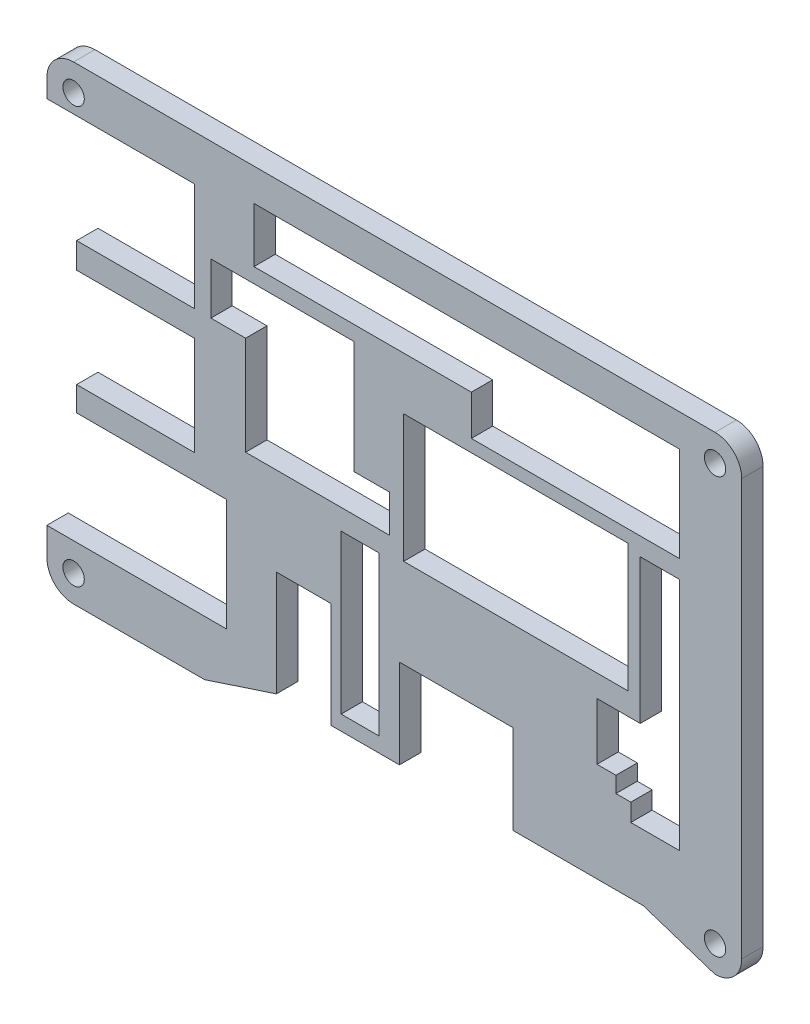
SolidWorks part; units mm, degrees
ref_plane "Front Plane" through (0, 0, 0) normal (0, 0, 1) x (1, 0, 0)
ref_plane "Top Plane" through (0, 0, 0) normal (0, 1, 0) x (1, 0, 0)
ref_plane "Right Plane" through (0, 0, 0) normal (1, 0, 0) x (0, 0, -1)
sketch "Sketch2" plane through (0, 0, 8.1718) normal (0, 0, -1) x (-1, 0, 0)
  line L0 (-23.8449, -33.0844) -> (-34.0849, -36.451) construction
  line L1 (-37.8949, -32.641) -> (-37.8949, 26.6977) construction
  line L2 (-34.0849, 30.5077) -> (57.4049, 30.5077) construction
  line L3 (61.2149, 26.6839) -> (61.2149, 24.0683) construction
  line L4 (56.975, 8.6582) -> (56.975, 4.9979) construction
  line L5 (56.975, -9.1218) -> (56.975, -12.628) construction
  line L6 (61.2149, -28.6278) -> (61.2149, -32.6134) construction
  line L7 (38.7143, -36.451) -> (57.405, -36.451) construction
  line L8 (28.4743, -33.0844) -> (38.7143, -36.451) construction
  line L9 (-23.8449, -33.0844) -> (-34.0849, -36.451)
  line L10 (-37.8949, -32.641) -> (-37.8949, 26.6977)
  line L11 (-34.0849, 30.5077) -> (57.4049, 30.5077)
  line L12 (61.2149, 26.6839) -> (61.2149, 24.0683)
  line L13 (56.975, 8.6582) -> (56.975, 4.9979)
  line L14 (56.975, -9.1218) -> (56.975, -12.628)
  line L15 (61.2149, -28.6278) -> (61.2149, -32.6134)
  line L16 (38.7143, -36.451) -> (57.405, -36.451)
  line L17 (28.4743, -33.0844) -> (38.7143, -36.451)
  line L18 (-23.8449, -33.0844) -> (-5.3029, -33.0844)
  line L19 (-5.3029, -33.0844) -> (-5.3029, -20.3844)
  line L20 (-5.3029, -20.3844) -> (10.9264, -20.3844)
  line L21 (10.9264, -16.0062) -> (10.9264, -22.1276) construction
  line L22 (10.9264, -20.3844) -> (10.9264, -33.0844)
  line L23 (10.9264, -33.0844) -> (20.6581, -33.0844)
  line L24 (20.6581, -33.0844) -> (20.6581, -18.0349)
  line L25 (20.6581, -18.0349) -> (28.4743, -18.0349)
  line L26 (28.4743, -18.0349) -> (28.4743, -33.0844)
  line L27 (13.845, -30.9668) -> (19.2484, -30.9668)
  line L28 (20.6581, -30.9668) -> (13.845, -30.9668) construction
  line L29 (19.2484, -30.9668) -> (19.2484, -8.3602)
  line L30 (19.2484, -8.3602) -> (13.845, -8.3602)
  line L31 (13.845, -8.3602) -> (13.845, -30.9668)
  line L32 (-29.0049, -23.6989) -> (-22.0669, -23.6989) construction
  line L33 (-22.0669, -21.1858) -> (-22.0669, -23.6989) construction
  line L34 (-19.9509, -21.1858) -> (-22.0669, -21.1858) construction
  line L35 (-19.9509, -18.9206) -> (-19.9509, -21.1858) construction
  line L36 (-17.2447, -18.9206) -> (-19.9509, -18.9206) construction
  line L37 (-17.2447, -10.7926) -> (-17.2447, -18.9206) construction
  line L38 (-23.4169, -10.7926) -> (-17.2447, -10.7926) construction
  line L39 (-23.4169, 9.8012) -> (-23.4169, -10.7926) construction
  line L40 (-29.0049, 9.8012) -> (-29.0049, -23.6989) construction
  line L41 (-23.4169, 9.8012) -> (-29.0049, 9.8012) construction
  line L42 (-29.0049, -23.6989) -> (-22.0669, -23.6989)
  line L43 (-22.0669, -21.1858) -> (-22.0669, -23.6989)
  line L44 (-19.9509, -21.1858) -> (-22.0669, -21.1858)
  line L45 (-19.9509, -18.9206) -> (-19.9509, -21.1858)
  line L46 (-17.2447, -18.9206) -> (-19.9509, -18.9206)
  line L47 (-17.2447, -10.7926) -> (-17.2447, -18.9206)
  line L48 (-23.4169, -10.7926) -> (-17.2447, -10.7926)
  line L49 (-23.4169, 9.8012) -> (-23.4169, -10.7926)
  line L50 (-29.0049, 9.8012) -> (-29.0049, -23.6989)
  line L51 (-23.4169, 9.8012) -> (-29.0049, 9.8012)
  line L52 (-21.6389, 10.5941) -> (-21.6389, -7.643) construction
  line L53 (-21.6389, 10.5941) -> (10.329, 10.5941) construction
  line L54 (12.361, -0.0976) -> (17.441, -0.0976) construction
  line L55 (12.361, -0.0976) -> (12.361, -5.4315) construction
  line L56 (37.825, 8.6582) -> (32.872, 8.6582) construction
  line L57 (37.825, 15.9724) -> (37.825, 8.6582) construction
  line L58 (17.441, 15.9724) -> (37.825, 15.9724) construction
  line L59 (17.441, 15.9724) -> (17.441, -0.0976) construction
  line L60 (-21.6389, 10.5941) -> (-21.6389, -7.643)
  line L61 (-21.6389, 10.5941) -> (10.329, 10.5941)
  line L62 (12.361, -0.0976) -> (17.441, -0.0976)
  line L63 (12.361, -0.0976) -> (12.361, -5.4315)
  line L64 (37.825, 8.6582) -> (32.872, 8.6582)
  line L65 (37.825, 15.9724) -> (37.825, 8.6582)
  line L66 (17.441, 15.9724) -> (37.825, 15.9724)
  line L67 (17.441, 15.9724) -> (17.441, -0.0976)
  line L68 (32.872, 8.6582) -> (32.872, -5.4315)
  line L69 (12.361, -5.4315) -> (33.38, -5.4315) construction
  line L70 (32.872, -5.4315) -> (12.361, -5.4315)
  line L71 (-21.6389, -7.643) -> (10.329, -7.643)
  line L72 (10.329, 10.5941) -> (10.329, -9.6302) construction
  line L73 (10.329, -7.643) -> (10.329, 10.5941)
  line L74 (0.6771, 12.3721) -> (-29.0048, 12.3721)
  line L75 (-29.0049, 25.897) -> (-29.0048, 12.0872) construction
  line L76 (-29.0048, 12.3721) -> (-29.0049, 25.897)
  line L77 (-29.0049, 25.897) -> (31.6883, 25.897)
  line L78 (31.6883, 25.897) -> (31.6883, 18.087)
  line L79 (31.6883, 18.087) -> (0.6771, 18.087)
  line L80 (0.6771, 18.087) -> (0.6771, 12.3721)
  line L81 (40.1348, -9.1218) -> (40.1348, 4.9979)
  line L82 (40.1348, 4.9979) -> (56.975, 4.9979)
  line L83 (40.1348, 24.0683) -> (61.2149, 24.0683)
  line L84 (56.975, 8.6582) -> (40.1348, 8.6582)
  line L85 (40.1348, 8.6582) -> (40.1348, 24.0683)
  line L86 (35.285, -9.1218) -> (56.975, -9.1218) construction
  line L87 (40.1348, -9.1218) -> (56.975, -9.1218)
  line L88 (61.2149, -28.6278) -> (35.575, -28.6278)
  line L89 (35.575, -28.6278) -> (35.575, -12.628)
  line L90 (56.975, -12.628) -> (33.9353, -12.628) construction
  line L91 (35.575, -12.628) -> (56.975, -12.628)
  arc A0 (-37.8949, -32.641) -> (-34.0849, -36.451) centre (-34.0849, -32.641) ccw construction
  arc A1 (-34.0849, 30.5077) -> (-37.8949, 26.6977) centre (-34.0849, 26.6977) ccw construction
  arc A2 (61.2149, 26.6839) -> (57.4049, 30.5077) centre (57.4049, 26.6977) ccw construction
  arc A3 (57.405, -36.451) -> (61.2149, -32.6134) centre (57.405, -32.641) ccw construction
  arc A4 (-37.8949, -32.641) -> (-34.0849, -36.451) centre (-34.0849, -32.641) ccw
  arc A5 (-34.0849, 30.5077) -> (-37.8949, 26.6977) centre (-34.0849, 26.6977) ccw
  arc A6 (61.2149, 26.6839) -> (57.4049, 30.5077) centre (57.4049, 26.6977) ccw
  arc A7 (57.405, -36.451) -> (61.2149, -32.6134) centre (57.405, -32.641) ccw
  dimension "D1" = 12.7
  dimension "D2" = 1.4097
  dimension "D3" = 15.0495
  dimension "D4" = 16.8402
  dimension "D5" = 16.8402
extrude "Boss-Extrude1" add sketch "Sketch2" along normal blind 3.048
sketch "Sketch3" plane through (0, 0, 5.1238) normal (0, 0, -1) x (-1, 0, 0)
  circle A0 centre (57.405, -32.641) radius 1.3382
  circle A1 centre (-34.0849, -32.641) radius 1.3382
  circle A2 centre (-34.0849, 26.6977) radius 1.3382
  circle A3 centre (57.4049, 26.6977) radius 1.3382
  dimension "D1" = 2.6765
extrude "Cut-Extrude1" cut sketch "Sketch3" against normal through all
sketch "Sketch4" plane through (0, 0, 5.1238) normal (0, 0, -1) x (-1, 0, 0)
  circle A0 centre (-34.0849, 26.6977) radius 1.524
  circle A1 centre (-34.0849, -32.641) radius 1.524
  circle A2 centre (57.405, -32.641) radius 1.524
  circle A3 centre (57.4049, 26.6977) radius 1.524
  dimension "D1" = 3.048
extrude "Cut-Extrude2" cut sketch "Sketch4" against normal through all
